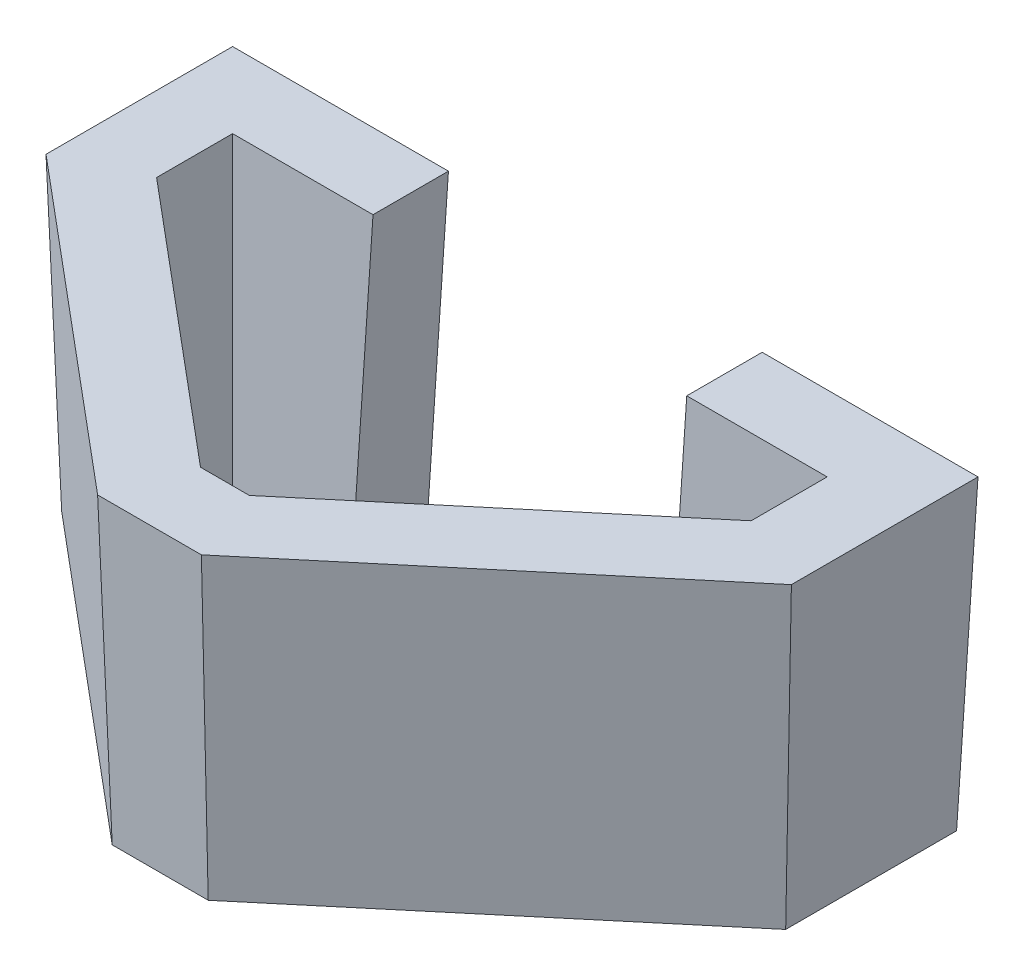
SolidWorks part; units mm, degrees
ref_plane "Alzado" through (0, 0, 0) normal (0, 0, 1) x (1, 0, 0)
ref_plane "Planta" through (0, 0, 0) normal (0, 1, 0) x (1, 0, 0)
ref_plane "Vista lateral" through (0, 0, 0) normal (1, 0, 0) x (0, 0, -1)
sketch "Croquis0" plane through (0, 0, 0) normal (1, 0, 0) x (0, 0, -1)
  line L0 (0, 0) -> (0, 100) construction
  line L1 (0, 0) -> (-3.4921, 100)
  dimension "D1" = 2
  dimension "D2" = 100
  dimension "D3" = 100
sketch "Croquis2" plane through (0, 0, 0) normal (0, 1, 0) x (1, 0, 0)
  line L0 (0, 0) -> (95, 0) construction
  line L1 (95, 0) -> (95, -10) construction
  line L2 (95, -10) -> (50.9051, -47) construction
  line L3 (50.9051, -47) -> (44.0949, -47) construction
  line L4 (44.0949, -47) -> (0, -10) construction
  line L5 (0, -10) -> (0, 0) construction
  line L6 (47.5, 0) -> (47.5, -100.0838) construction
  line L7 (0, -10) -> (14.9783, -10) construction
  line L8 (-12.5, 12.5) -> (107.5, 12.5)
  line L9 (107.5, 12.5) -> (107.5, -15.8288)
  line L10 (107.5, -15.8288) -> (55.4547, -59.5)
  line L11 (55.4547, -59.5) -> (39.5453, -59.5)
  line L12 (39.5453, -59.5) -> (-12.5, -15.8288)
  line L13 (-12.5, -15.8288) -> (-12.5, 12.5)
  dimension "D1" = 95
  dimension "D2" = 10
  dimension "D3" = 47
  dimension "D4" = 40
  dimension "D5" = 12.5
extrude "Saliente-Extruir1" add sketch "Croquis2" along normal blind 50.8 draft 2 draft outward yes
sketch "Croquis3" plane through (0, 50.8, 0) normal (0, 1, 0) x (1, 0, 0)
  line L12 (-1.774, 1.774) -> (-1.774, -10.8272)
  line L13 (-1.774, -10.8272) -> (43.4492, -48.774)
  line L14 (43.4492, -48.774) -> (51.5508, -48.774)
  line L15 (51.5508, -48.774) -> (96.774, -10.8272)
  line L16 (96.774, -10.8272) -> (96.774, 1.774)
  line L17 (96.774, 1.774) -> (-1.774, 1.774)
  line L18 (-1.774, 1.774) -> (-1.774, -10.8272)
  line L19 (-1.774, -10.8272) -> (43.4492, -48.774)
  line L20 (43.4492, -48.774) -> (51.5508, -48.774)
  line L21 (51.5508, -48.774) -> (96.774, -10.8272)
  line L22 (96.774, -10.8272) -> (96.774, 1.774)
  line L23 (96.774, 1.774) -> (-1.774, 1.774)
  dimension "D1" = 12.5
extrude "Cortar-Extruir1" cut sketch "Croquis3" against normal blind 50.8 draft 2
sketch "Croquis4" plane through (0, 50.8, 0) normal (0, 1, 0) x (1, 0, 0)
  line L6 (-14.274, 14.274) -> (-14.274, -16.6561)
  line L7 (-14.274, -16.6561) -> (38.8996, -61.274)
  line L8 (38.8996, -61.274) -> (56.1004, -61.274)
  line L9 (56.1004, -61.274) -> (109.274, -16.6561)
  line L10 (109.274, -16.6561) -> (109.274, 14.274)
  line L11 (109.274, 14.274) -> (-14.274, 14.274)
  line L12 (-14.274, 14.274) -> (-14.274, -16.6561)
  line L13 (-14.274, -16.6561) -> (38.8996, -61.274)
  line L14 (38.8996, -61.274) -> (56.1004, -61.274)
  line L15 (56.1004, -61.274) -> (109.274, -16.6561)
  line L16 (109.274, -16.6561) -> (109.274, 14.274)
  line L17 (109.274, 14.274) -> (-14.274, 14.274)
  dimension "D1" = 0
sketch "Croquis5" plane through (0, 50.8, 0) normal (0, -1, 0) x (1, 0, 0)
  line L1 (109.274, -14.274) -> (-14.274, -14.274) construction
  line L2 (21.5, -1.774) -> (21.5, -14.274)
  line L5 (21.5, -14.274) -> (73.5, -14.274)
  line L18 (73.5, -14.274) -> (73.5, -1.774)
  line L19 (73.5, -1.774) -> (21.5, -1.774)
  line L22 (96.774, -1.774) -> (-1.774, -1.774) construction
  line L24 (43.4492, 48.774) -> (51.5508, 48.774) construction
  point P10 (47.5, 48.774)
  point P11 (47.5, -1.774)
  dimension "D1" = 52
extrude "Cortar-Extruir2" cut sketch "Croquis5" along direction (0.0349, 0.9988, -0.0349) on the side of the normal through all
sketch "Croquis6" plane through (0, 50.8, 0) normal (0, 1, 0) x (1, 0, 0)
  line L0 (-14.274, 14.274) -> (-1.774, 1.774)
  line L1 (96.774, 1.774) -> (109.274, 14.274)
  line L2 (-1.774, -10.8272) -> (-1.774, -27.1448)
  line L3 (96.774, -10.8272) -> (96.774, -27.1448)
  line L4 (24.0027, -48.774) -> (70.9973, -48.774)
  line L5 (43.4492, -48.774) -> (51.5508, -48.774) construction
  line L7 (-14.274, -16.6561) -> (38.8996, -61.274) construction
  line L8 (56.1004, -61.274) -> (109.274, -16.6561) construction
  line L9 (21.5, 1.774) -> (21.5, 14.274) construction
  line L10 (73.5, 14.274) -> (73.5, 1.774) construction
  line L11 (73.5, 14.274) -> (73.5, 1.774)
  line L12 (21.5, 1.774) -> (21.5, 14.274)
  dimension "D1" = 35.774
  dimension "D2" = 52
sketch "Croquis7" plane through (0, 0, 0) normal (0, -1, 0) x (1, 0, 0)
  line L0 (-12.5, -12.5) -> (0, 0)
  line L1 (0, 10) -> (0, 26.3176)
  line L2 (-12.5, 15.8288) -> (39.5453, 59.5) construction
  line L3 (107.5, -12.5) -> (95, 0)
  line L4 (95, 10) -> (95, 26.3176)
  line L5 (55.4547, 59.5) -> (107.5, 15.8288) construction
  line L6 (24.6483, 47) -> (70.3517, 47)
  line L7 (44.0949, 47) -> (50.9051, 47) construction
  line L12 (71.726, 0) -> (71.726, -12.5) construction
  line L13 (19.726, -12.5) -> (19.726, 0) construction
  line L14 (71.726, 0) -> (71.726, -12.5)
  line L15 (19.726, -12.5) -> (19.726, 0)
  point P25 (7.9279, 0.7417)
  dimension "D1" = 32.226
  dimension "D2" = 17.6777
